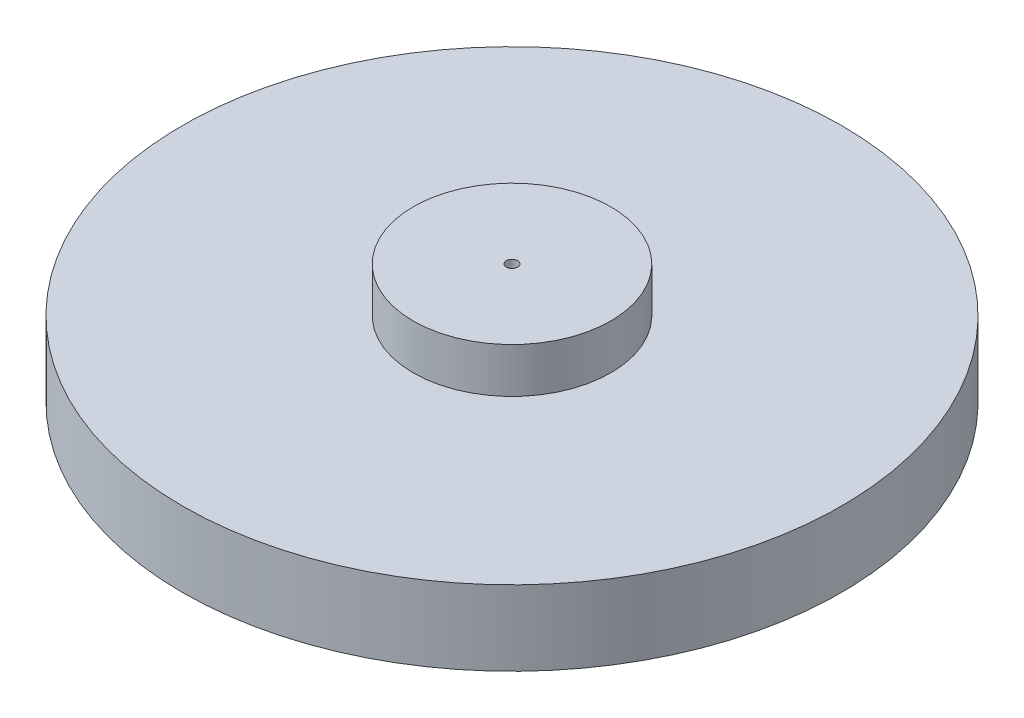
SolidWorks part; units mm, degrees
material "6061-T6 (SS)"
ref_plane "Front Plane" through (0, 0, 0) normal (0, 0, 1) x (1, 0, 0)
ref_plane "Top Plane" through (0, 0, 0) normal (0, 1, 0) x (1, 0, 0)
ref_plane "Right Plane" through (0, 0, 0) normal (1, 0, 0) x (0, 0, -1)
sketch "Sketch1" plane through (0, 0, 0) normal (0, 1, 0) x (1, 0, 0)
  circle A0 centre (0, 0) radius 69.85
  dimension "D1" = 139.7
extrude "Boss-Extrude1" add sketch "Sketch1" along normal blind 15.875
sketch "Sketch2" plane through (0, 15.875, 0) normal (0, 1, 0) x (1, 0, 0)
  circle A1 centre (0, 0) radius 20.955
  dimension "D2" = 41.91
extrude "Boss-Extrude2" add sketch "Sketch2" along normal blind 9.525
sketch "Sketch13" plane through (0, 0, 0) normal (0, -1, 0) x (1, 0, 0)
  circle A0 centre (0, 0) radius 14.2875
  circle A1 centre (0, 0) radius 25.4
  circle A2 centre (0, 0) radius 33.02
  circle A3 centre (0, 0) radius 41.275
  circle A4 centre (0, 0) radius 7.62
  dimension "D1" = 28.575
  dimension "D2" = 50.8
  dimension "D3" = 66.04
  dimension "D4" = 82.55
  dimension "D5" = 15.24
extrude "Cut-Extrude10" cut sketch "Sketch13" against normal blind 6.35 contours A3 A2 | A1 A0 | A4
sketch "Sketch14" plane through (0, 6.35, 0) normal (0, -1, 0) x (1, 0, 0)
  circle A0 centre (0, 0) radius 1.1906
  dimension "D1" = 2.3813
extrude "Cut-Extrude11" cut sketch "Sketch14" against normal through all
